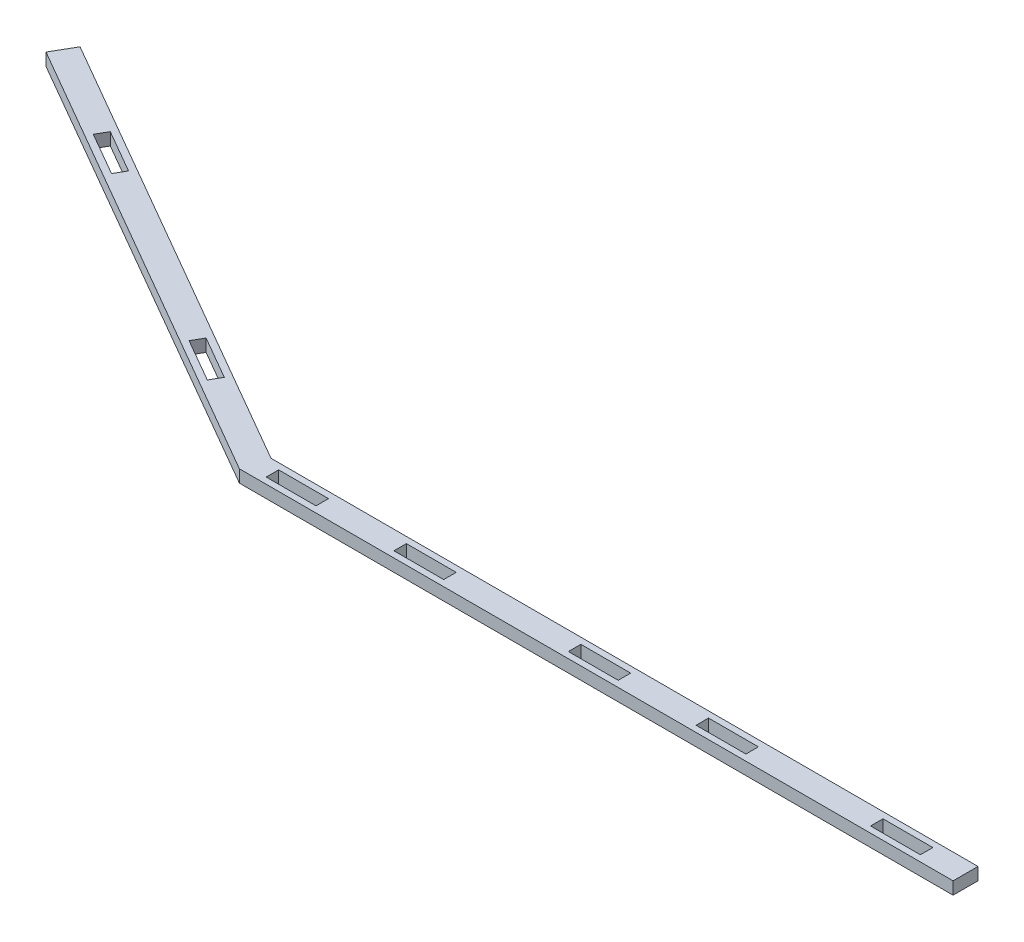
SolidWorks part; units mm, degrees
material "Cedar"
ref_plane "Front Plane" through (0, 0, 0) normal (0, 0, 1) x (1, 0, 0)
ref_plane "Top Plane" through (0, 0, 0) normal (0, 1, 0) x (1, 0, 0)
ref_plane "Right Plane" through (0, 0, 0) normal (1, 0, 0) x (0, 0, -1)
sketch "Sketch4" plane through (0, 0, 0) normal (0, 1, 0) x (1, 0, 0)
  line L0 (-596.8496, 128.2761) -> (-590.4996, 139.2746)
  line L1 (-590.4996, 139.2746) -> (-360.2674, 6.35)
  line L2 (-596.8496, 128.2761) -> (-363.6704, -6.35)
  line L3 (0, -6.35) -> (0, 6.35)
  line L4 (0, 6.35) -> (-360.2674, 6.35)
  line L5 (0, -6.35) -> (-363.6704, -6.35)
  line L6 (-548.5184, 104.0382) -> (-526.5214, 91.3382)
  line L7 (-526.5214, 91.3382) -> (-523.3464, 96.8375)
  line L8 (-523.3464, 96.8375) -> (-545.3434, 109.5375)
  line L9 (-545.3434, 109.5375) -> (-548.5184, 104.0382)
  line L10 (-433.0339, 37.3632) -> (-411.0369, 24.6632)
  line L11 (-411.0369, 24.6632) -> (-407.8619, 30.1625)
  line L12 (-407.8619, 30.1625) -> (-429.8589, 42.8625)
  line L13 (-429.8589, 42.8625) -> (-433.0339, 37.3632)
  line L14 (-353.1983, 3.175) -> (-353.1983, -3.175)
  line L15 (-353.1983, -3.175) -> (-327.7983, -3.175)
  line L16 (-327.7983, -3.175) -> (-327.7983, 3.175)
  line L17 (-327.7983, 3.175) -> (-353.1983, 3.175)
  line L18 (-288.119, 3.175) -> (-288.119, -3.175)
  line L19 (-288.119, -3.175) -> (-262.719, -3.175)
  line L20 (-262.719, -3.175) -> (-262.719, 3.175)
  line L21 (-262.719, 3.175) -> (-288.119, 3.175)
  line L22 (-173.819, -3.175) -> (-173.819, 3.175)
  line L23 (-173.819, 3.175) -> (-199.219, 3.175)
  line L24 (-199.219, 3.175) -> (-199.219, -3.175)
  line L25 (-199.219, -3.175) -> (-173.819, -3.175)
  line L26 (-134.1397, 3.175) -> (-134.1397, -3.175)
  line L27 (-134.1397, -3.175) -> (-108.7397, -3.175)
  line L28 (-108.7397, -3.175) -> (-108.7397, 3.175)
  line L29 (-108.7397, 3.175) -> (-134.1397, 3.175)
  line L30 (-19.8397, -3.175) -> (-19.8397, 3.175)
  line L31 (-19.8397, 3.175) -> (-45.2397, 3.175)
  line L32 (-45.2397, 3.175) -> (-45.2397, -3.175)
  line L33 (-45.2397, -3.175) -> (-19.8397, -3.175)
  point P34 (0, 0)
  dimension "D1" = 12.7
  dimension "D2" = 363.6704
  dimension "D3" = 360.2674
  dimension "D4" = 265.8493
  dimension "D5" = 269.2522
  dimension "D6" = 12.7
  dimension "D7" = 53.975
  dimension "D8" = 6.35
  dimension "D9" = 25.4
  dimension "D10" = 3.175
  dimension "D11" = 25.4
  dimension "D12" = 6.35
  dimension "D13" = 107.95
  dimension "D14" = 25.4
  dimension "D15" = 6.35
  dimension "D16" = 25.4
  dimension "D17" = 6.35
  dimension "D18" = 3.175
  dimension "D19" = 19.8397
  dimension "D20" = 25.4
  dimension "D21" = 6.35
  dimension "D22" = 25.4
  dimension "D23" = 6.35
  dimension "D24" = 3.175
  dimension "D25" = 63.5
  dimension "D26" = 6.35
  dimension "D27" = 25.4
  dimension "D28" = 6.35
  dimension "D29" = 25.4
  dimension "D30" = 3.175
  dimension "D31" = 39.6793
  dimension "D32" = 6.35
  dimension "D33" = 25.4
  dimension "D34" = 6.35
  dimension "D35" = 25.4
  dimension "D36" = 3.175
  dimension "D37" = 63.5
  dimension "D38" = 6.35
  dimension "D39" = 25.4
  dimension "D40" = 6.35
  dimension "D41" = 25.4
  dimension "D42" = 3.175
  dimension "D43" = 39.6793
  dimension "D44" = 6.35
  dimension "D45" = 25.4
  dimension "D46" = 6.35
  dimension "D47" = 25.4
  dimension "D48" = 3.175
extrude "Boss-Extrude2" add sketch "Sketch4" along normal blind 6.35
